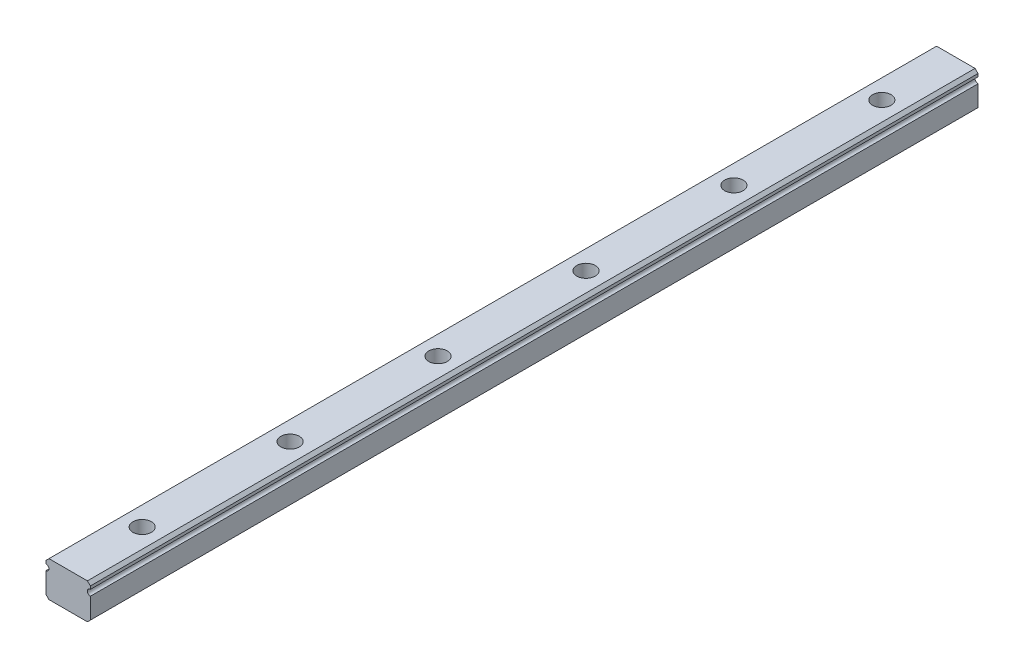
SolidWorks part; units mm, degrees
ref_plane "Front" through (0, 0, 0) normal (0, 0, 1) x (1, 0, 0)
ref_plane "Top" through (0, 0, 0) normal (0, 1, 0) x (1, 0, 0)
ref_plane "Right" through (0, 0, 0) normal (1, 0, 0) x (0, 0, -1)
sketch "Sketch1" plane through (0, 0, 0) normal (0, 0, 1) x (1, 0, 0)
  line L0 (-1.5, 1) -> (-1.3, 1.2)
  line L1 (-1.3, -1.2) -> (1.3, -1.2)
  line L2 (-1.5, -1) -> (-1.5, 0.4)
  line L3 (-1.3, 1.2) -> (1.3, 1.2)
  line L4 (1.5, -1) -> (1.5, 0.4)
  line L5 (0, -1.2) -> (0, 1.2) construction
  line L6 (1.5, 0) -> (-1.5, 0) construction
  line L7 (-1.5, 0.8) -> (-1.5, 1)
  line L8 (1.5, 0.8) -> (1.5, 1)
  line L9 (-1.5, -1) -> (-1.3, -1.2)
  line L10 (1.5, -1) -> (1.3, -1.2)
  line L11 (1.5, 1) -> (1.3, 1.2)
  arc A0 (-1.5, 0.4) -> (-1.5, 0.8) centre (-1.5, 0.6) ccw
  arc A1 (1.5, 0.4) -> (1.5, 0.8) centre (1.5, 0.6) cw
  point P0 (0, 0)
  dimension "D6" = 0.2
  dimension "D1" = 3
  dimension "D2" = 2.4
  dimension "D3" = 0.6
  dimension "D4" = 45
  dimension "D5" = 0.2
extrude "Boss-Extrude1" add sketch "Sketch1" along normal blind 60
hole_wizard "M1.6x0.35 Tapped Hole1" positions "Sketch2" profile "Sketch3" tap size "M1.6x0.35" standard "ANSI Metric" end condition up to next
sketch "Sketch2" plane through (0, 1.2, 0) normal (0, 1, 0) x (1, 0, 0)
  point P0 (0, -5)
  dimension "D1" = 5
sketch "Sketch3" plane through (0, 1.2, 5) normal (1, 0, 0) x (0, 0, 1)
  line L0 (0, 0) -> (0, 2.4)
  line L1 (0, 2.4) -> (0.625, 2.4)
  line L2 (0.625, 2.4) -> (0.625, 0)
  line L5 (0.625, 0) -> (0, 0)
  line L11 (0, -6.35) -> (0, 107.95) construction
  dimension "Thru Tap Drill Dia." = 1.25
  dimension "Thru Tap Drill Depth" = 2.4
cosmetic thread "Hole Thread1" parameters "D2"=1.6
pattern_linear "LPattern1" count 6 spacing 10 along (0, 0, 1) of "M1.6x0.35 Tapped Hole1"
cosmetic thread "Hole Thread2" parameters "D2"=1.6
cosmetic thread "Hole Thread3" parameters "D2"=1.6
cosmetic thread "Hole Thread4" parameters "D2"=1.6
cosmetic thread "Hole Thread5" parameters "D2"=1.6
cosmetic thread "Hole Thread6" parameters "D2"=1.6
